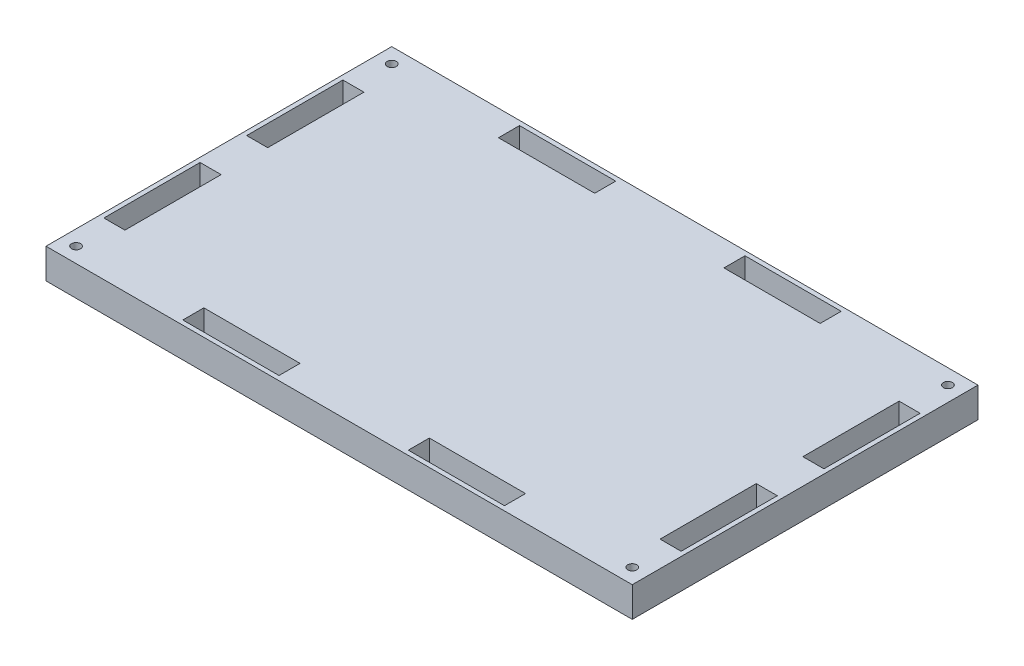
SolidWorks part; units mm, degrees
ref_plane "Plano frontal" through (0, 0, 0) normal (0, 0, 1) x (1, 0, 0)
ref_plane "Plano superior" through (0, 0, 0) normal (0, 1, 0) x (1, 0, 0)
ref_plane "Plano direito" through (0, 0, 0) normal (1, 0, 0) x (0, 0, -1)
sketch "Esboço1" plane through (0, 0, 0) normal (0, 1, 0) x (1, 0, 0)
  line L1 (97.5, -57.5) -> (-97.5, -57.5)
  line L2 (97.5, -57.5) -> (97.5, 57.5)
  line L3 (97.5, 57.5) -> (-97.5, 57.5)
  line L4 (-97.5, -57.5) -> (-97.5, 57.5)
  line L5 (97.5, -57.5) -> (-97.5, 57.5) construction
  line L6 (97.5, 57.5) -> (-97.5, -57.5) construction
  point P0 (0, 0)
  dimension "D1" = 195
  dimension "D2" = 115
extrude "Ressalto-extrusão1" add sketch "Esboço1" along normal blind 10
sketch "Esboço2" plane through (0, 10, 0) normal (0, 1, 0) x (1, 0, 0)
  line L0 (0, -86.5716) -> (0, 73.7054) construction
  line L1 (-137.4853, 0) -> (143.3671, 0) construction
  line L2 (-97.5, -57.5) -> (97.5, -57.5) construction
  line L3 (-21.5, -56) -> (-53.5, -56)
  line L4 (-21.5, -56) -> (-21.5, -49)
  line L5 (-21.5, -49) -> (-53.5, -49)
  line L6 (-53.5, -56) -> (-53.5, -49)
  line L7 (-21.5, -56) -> (-53.5, -49) construction
  line L8 (-21.5, -49) -> (-53.5, -56) construction
  line L9 (-97.5, 57.5) -> (-97.5, -57.5) construction
  line L10 (21.5, -56) -> (21.5, -49)
  line L11 (21.5, -56) -> (53.5, -56)
  line L12 (53.5, -56) -> (53.5, -49)
  line L13 (21.5, -49) -> (53.5, -49)
  line L14 (53.5, 56) -> (53.5, 49)
  line L15 (21.5, 56) -> (53.5, 56)
  line L16 (21.5, 56) -> (21.5, 49)
  line L17 (21.5, 49) -> (53.5, 49)
  line L18 (-21.5, 56) -> (-21.5, 49)
  line L19 (-21.5, 56) -> (-53.5, 56)
  line L20 (-53.5, 56) -> (-53.5, 49)
  line L21 (-21.5, 49) -> (-53.5, 49)
  line L22 (97.5, 57.5) -> (-97.5, 57.5) construction
  line L23 (-89, 7.75) -> (-96, 7.75)
  line L24 (-89, 7.75) -> (-89, 39.75)
  line L25 (-89, 39.75) -> (-96, 39.75)
  line L26 (-96, 7.75) -> (-96, 39.75)
  line L27 (-89, 7.75) -> (-96, 39.75) construction
  line L28 (-89, 39.75) -> (-96, 7.75) construction
  line L29 (-89, -7.75) -> (-96, -7.75)
  line L30 (-89, -7.75) -> (-89, -39.75)
  line L31 (-96, -7.75) -> (-96, -39.75)
  line L32 (-89, -39.75) -> (-96, -39.75)
  line L33 (89, -39.75) -> (96, -39.75)
  line L34 (89, -7.75) -> (89, -39.75)
  line L35 (96, -7.75) -> (96, -39.75)
  line L36 (89, -7.75) -> (96, -7.75)
  line L37 (89, 7.75) -> (96, 7.75)
  line L38 (89, 7.75) -> (89, 39.75)
  line L39 (96, 7.75) -> (96, 39.75)
  line L40 (89, 39.75) -> (96, 39.75)
  point P5 (-37.5, -52.5)
  point P18 (-21.5, -52.5)
  point P23 (-21.5, 52.5)
  point P28 (-92.5, 23.75)
  dimension "D1" = 32
  dimension "D2" = 7
  dimension "D3" = 1.5
  dimension "D4" = 60
  dimension "D5" = 32
  dimension "D6" = 7
  dimension "D7" = 1.5
  dimension "D8" = 33.75
extrude "Corte-extrusão2" cut sketch "Esboço2" against normal through all
sketch "Esboço3" plane through (0, 10, 0) normal (0, 1, 0) x (1, 0, 0)
  line L0 (97.5, 57.5) -> (-97.5, 57.5) construction
  line L1 (-97.5, 57.5) -> (-97.5, -57.5) construction
  line L2 (-160.8312, 0) -> (157.2176, 0) construction
  line L3 (0, 78.2819) -> (0, -84.7411) construction
  circle A0 centre (-92.5, 52.5) radius 1.5
  circle A1 centre (92.5, 52.5) radius 1.5
  circle A2 centre (92.5, -52.5) radius 1.5
  circle A3 centre (-92.5, -52.5) radius 1.5
  dimension "D1" = 3
  dimension "D2" = 5
  dimension "D3" = 5
extrude "Corte-extrusão3" cut sketch "Esboço3" against normal through all
